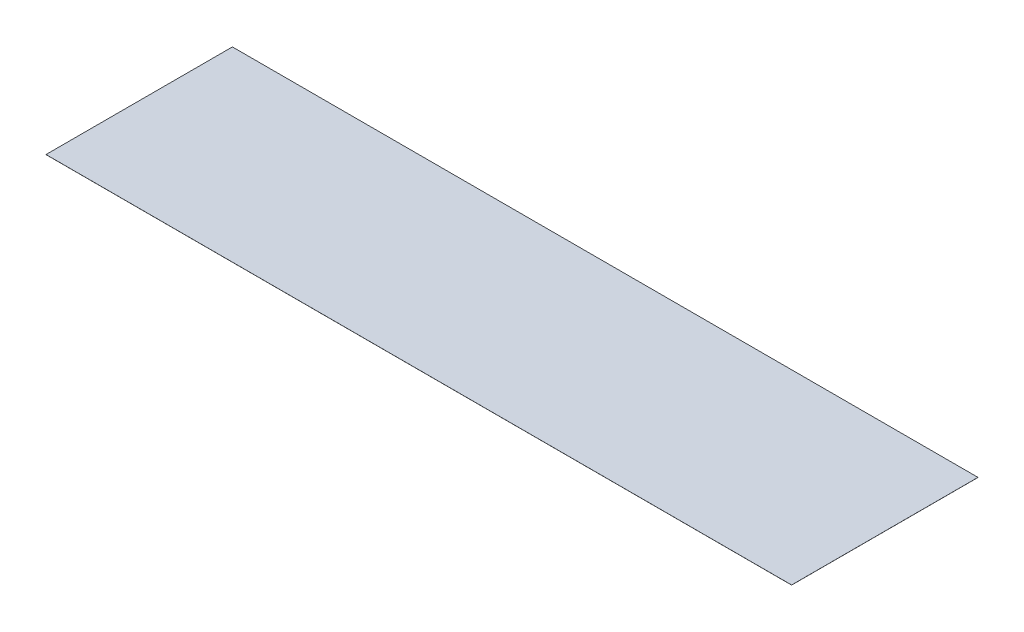
SolidWorks part; units mm, degrees
material "AISI 1020"
ref_plane "Front Plane" through (0, 0, 0) normal (0, 0, 1) x (1, 0, 0)
ref_plane "Top Plane" through (0, 0, 0) normal (0, 1, 0) x (1, 0, 0)
ref_plane "Right Plane" through (0, 0, 0) normal (1, 0, 0) x (0, 0, -1)
sketch "Sketch1" plane through (0, 0, 0) normal (0, 1, 0) x (1, 0, 0)
  line L1 (-4000, 1000) -> (4000, 1000)
  line L2 (-4000, 1000) -> (-4000, -1000)
  line L3 (-4000, -1000) -> (4000, -1000)
  line L4 (4000, 1000) -> (4000, -1000)
  line L5 (-4000, 1000) -> (4000, -1000) construction
  line L6 (-4000, -1000) -> (4000, 1000) construction
  point P0 (0, 0)
  dimension "D1" = 8000
  dimension "D2" = 2000
extrude "Boss-Extrude1" add sketch "Sketch1" along normal blind 1
sketch "Sketch2" plane through (0, 1, 0) normal (0, 1, 0) x (1, 0, 0)
  line L0 (-4000, 0) -> (4000, 0) construction
  line L1 (-4000, 1000) -> (-4000, -1000) construction
  line L2 (4000, -1000) -> (4000, 1000) construction
  point P3 (-3000, 0)
  point P4 (-1000, 0)
  point P7 (3000, 0)
  point P11 (1000, 0)
  dimension "D1" = 1000
  dimension "D2" = 2000
  dimension "D3" = 2000
  dimension "D4" = 2000
equation "\"dist_tub_center\" = 2000"
equation "\"D2@Sketch2\"=\"dist_tub_center\""
equation "\"D3@Sketch2\"=\"dist_tub_center\""
equation "\"D4@Sketch2\"=\"dist_tub_center\""
equation "\"edge_dist\"= 1000"
equation "\"D1@Sketch2\"=\"edge_dist\""
